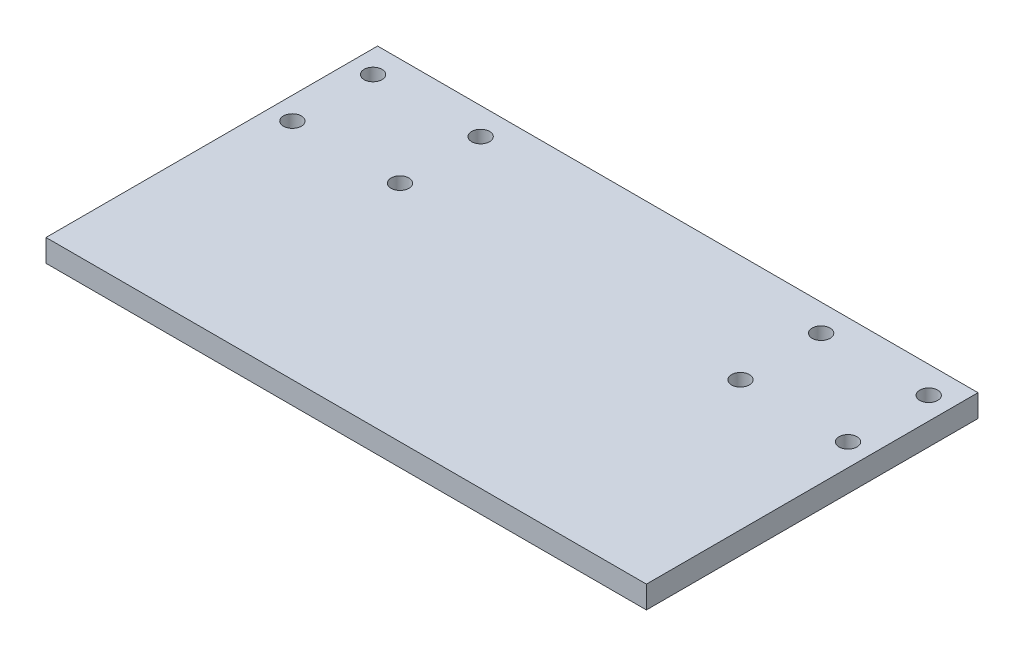
SolidWorks part; units mm, degrees
ref_plane "Front Plane" through (0, 0, 0) normal (0, 0, 1) x (1, 0, 0)
ref_plane "Top Plane" through (0, 0, 0) normal (0, 1, 0) x (1, 0, 0)
ref_plane "Right Plane" through (0, 0, 0) normal (1, 0, 0) x (0, 0, -1)
sketch "Sketch2" plane through (0, 0, 0) normal (0, 1, 0) x (1, 0, 0)
  line L1 (-57.9654, 61.5632) -> (76.0346, 61.5632)
  line L2 (-57.9654, 61.5632) -> (-57.9654, -12.4368)
  line L3 (-57.9654, -12.4368) -> (76.0346, -12.4368)
  line L4 (76.0346, 61.5632) -> (76.0346, -12.4368)
  dimension "D1" = 134
  dimension "D2" = 74
extrude "Boss-Extrude1" add sketch "Sketch2" along normal blind 5
sketch "Sketch3" plane through (0, 5, 0) normal (0, 1, 0) x (1, 0, 0)
  line L0 (76.0346, -12.4368) -> (76.0346, 61.5632) construction
  line L1 (76.0346, 61.5632) -> (-57.9654, 61.5632) construction
  circle A0 centre (71.0346, 55.5632) radius 2
  circle A1 centre (47.0346, 55.5549) radius 2
  circle A2 centre (71.0346, 37.5632) radius 2
  circle A3 centre (47.0346, 37.5549) radius 2
  circle A4 centre (-28.9654, 37.5632) radius 2
  circle A5 centre (-52.9654, 37.5549) radius 2
  circle A6 centre (-52.9654, 55.5549) radius 2
  circle A7 centre (-28.9654, 55.5632) radius 2
  dimension "D1" = 5
  dimension "D3" = 24
  dimension "D4" = 18
  dimension "D5" = 4
  dimension "D6" = 18
  dimension "D9" = 5
  dimension "D2" = 6
  dimension "D8" = 24
  dimension "D7" = 2
extrude "Cut-Extrude1" cut sketch "Sketch3" against normal through all
